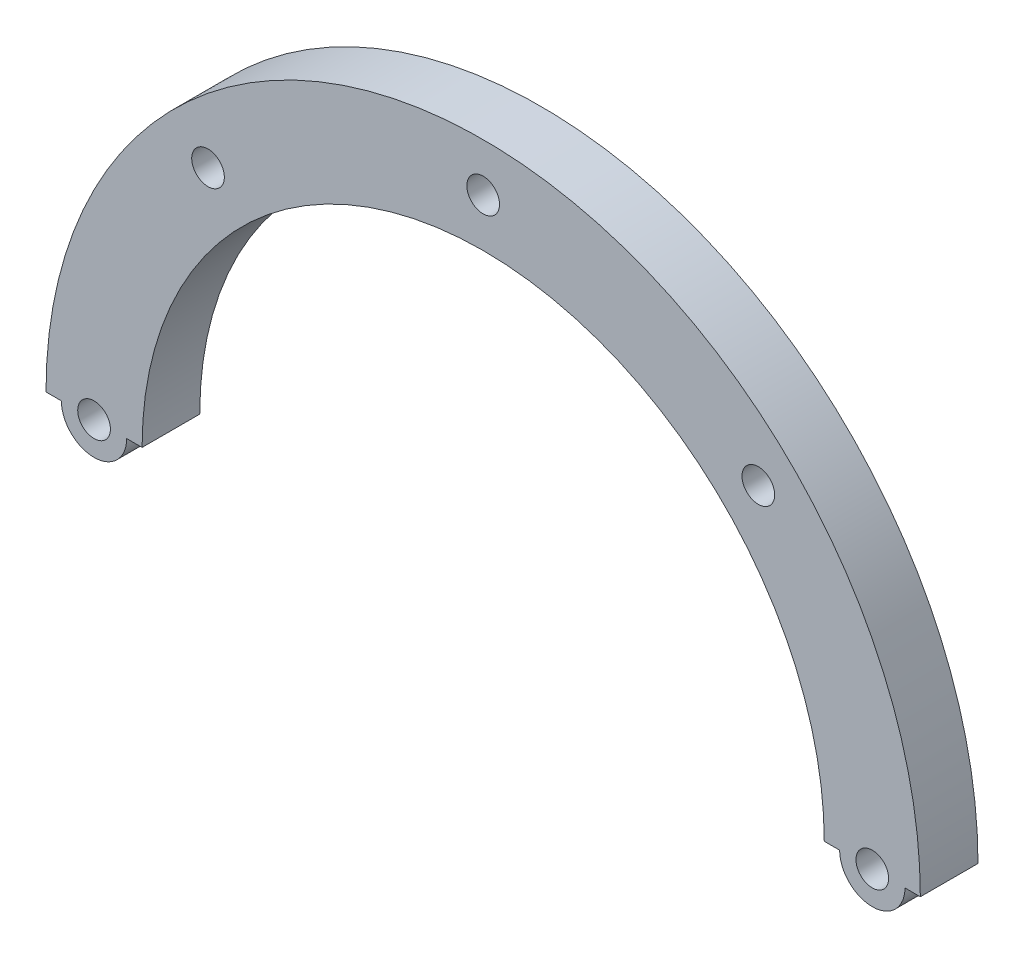
SolidWorks part; units mm, degrees
ref_plane "Alzado" through (0, 0, 0) normal (0, 0, 1) x (1, 0, 0)
ref_plane "Planta" through (0, 0, 0) normal (0, 1, 0) x (1, 0, 0)
ref_plane "Vista lateral" through (0, 0, 0) normal (1, 0, 0) x (0, 0, -1)
sketch "Croquis1" plane through (0, 0, 0) normal (0, 0, 1) x (1, 0, 0)
  line L0 (-45.5, 0) -> (-35.5, 0)
  line L1 (35.5, 0) -> (45.5, 0)
  arc A0 (35.5, 0) -> (-35.5, 0) centre (0, 0) ccw
  arc A1 (45.5, 0) -> (-45.5, 0) centre (0, 0) ccw
  circle A3 centre (0, 0) radius 45.5 construction
  circle A4 centre (0, 0) radius 35.5 construction
  point P6 (33.9488, 10.3792)
  point P7 (45.5, 0)
  dimension "D1" = 71
  dimension "D2" = 10
extrude "Saliente-Extruir1" add sketch "Croquis1" along normal blind 6
sketch "Croquis2" plane through (0, 0, 6) normal (0, 0, 1) x (1, 0, 0)
  line L1 (0, 35.5) -> (0, 45.5) construction
  circle A1 centre (0, 40.5) radius 1.7
  arc A2 (35.5, 0) -> (-35.5, 0) centre (0, 0) ccw construction
  arc A3 (45.5, 0) -> (-45.5, 0) centre (0, 0) ccw construction
  circle A4 centre (28.6378, 28.6378) radius 1.7
  circle A5 centre (40.5, 0) radius 1.7
  circle A6 centre (-40.5, 0) radius 1.7
  circle A7 centre (-28.6378, 28.6378) radius 1.7
  point P17 (0, 0)
  dimension "D1" = 3.4
  dimension "D2" = 3
extrude "Cortar-Extruir1" cut sketch "Croquis2" against normal through all
sketch "Croquis3" plane through (0, 0, 6) normal (0, 0, 1) x (1, 0, 0)
  line L0 (0, 0) -> (0, 9.7842) construction
  circle A0 centre (-40.5, 0) radius 3.4
  circle A1 centre (-40.5, 0) radius 1.7
  circle A2 centre (40.5, 0) radius 1.7
  circle A3 centre (40.5, 0) radius 3.4
  dimension "D1" = 6.8
extrude "Saliente-Extruir2" add sketch "Croquis3" against normal up to surface (6 mm away) up to face at (1.7, 40.5, 0)
